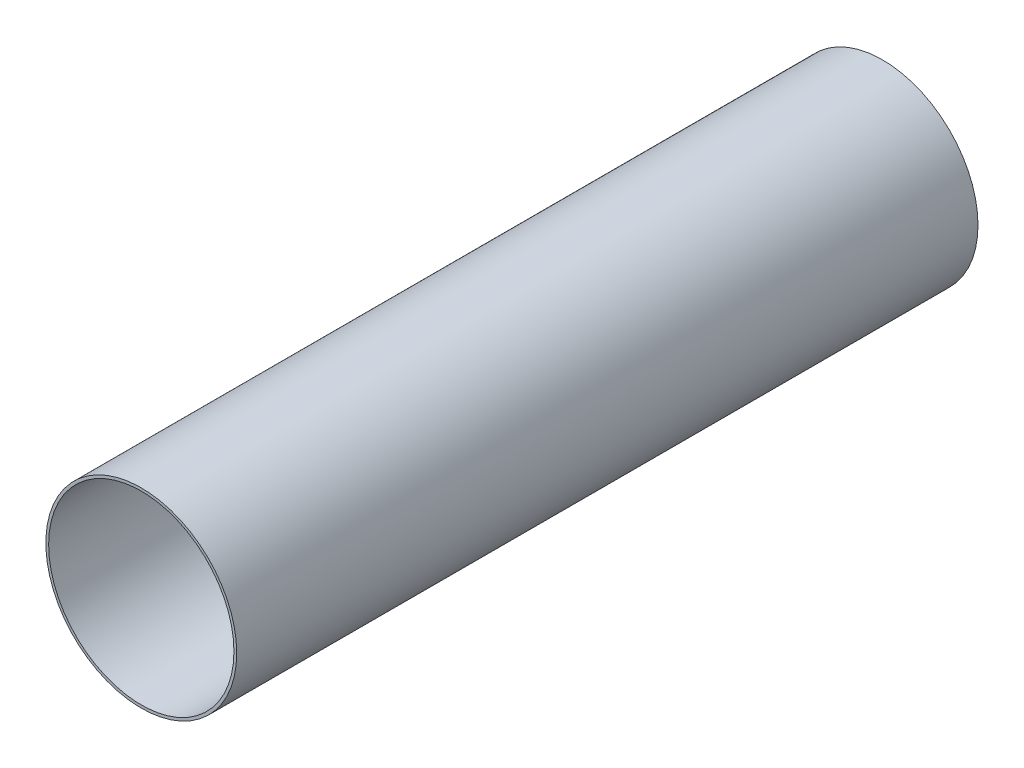
SolidWorks part; units mm, degrees
ref_plane "Front Plane" through (0, 0, 0) normal (0, 0, 1) x (1, 0, 0)
ref_plane "Top Plane" through (0, 0, 0) normal (0, 1, 0) x (1, 0, 0)
ref_plane "Right Plane" through (0, 0, 0) normal (1, 0, 0) x (0, 0, -1)
sketch "Sketch1" plane through (0, 0, 0) normal (0, 0, 1) x (1, 0, 0)
  circle A0 centre (0, 0) radius 65.405
  circle A1 centre (0, 0) radius 63.5
  dimension "D1" = 127
  dimension "D2" = 130.81
extrude "Boss-Extrude1" add sketch "Sketch1" along normal mid plane 508
equation "\"AIRFRAME_OD\"= 5.15in"
equation "\"AIRFRAME_ID\"= 5.00in"
equation "\"FLAT_T\"= 0.125in"
equation "\"NOSE_EXP_L\"= 27in"
equation "\"NOSE_SHOULDER_L\"= 5in"
equation "\"MAIN_L\"= 30in"
equation "\"RECO_COUP_L\"= 10in"
equation "\"RECO_SWITCH_L\"= 2in"
equation "\"DROGUE_L\"= 20in"
equation "\"ATS_FORE_COUP_L\"= 5.5in"
equation "\"ATS_AFT_COUP_L\"= 4.5in"
equation "\"LOWER_L\"= 30in"
equation "\"FIN_N\"= 4"
equation "\"CR_AFT_X\"= 0.5in"
equation "\"CR_FORE_X\"= 9.25in"
equation "\"D1@Sketch1\"=\"AIRFRAME_ID\""
equation "\"D2@Sketch1\"=\"AIRFRAME_OD\""
equation "\"D1@Boss-Extrude1\"=\"DROGUE_L\""
equation "\"FIN_ROOT\"= 8in"
equation "\"FIN_X\"= 0.75in"
equation "\"MOTOR_OD\"= 3.091in"
equation "\"MOTOR_ID\"= 3.00in"
equation "\"COUPLER_OD\"= 4.998in"
equation "\"COUPLER_ID\"= 4.88in"
equation "\"RECO_ROD_X\"= 3.5in"
equation "\"ATS_ROD_X\"= 3.75in"
equation "\"MOTOR_L\"= 14in"
equation "\"MOTOR_LOWER_X\"= 2in"
